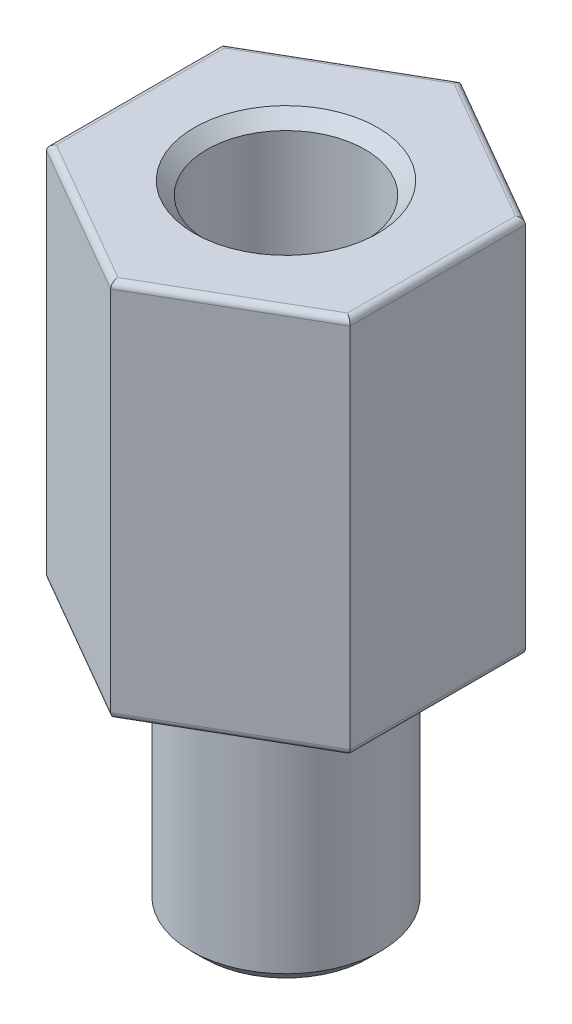
SolidWorks part; units mm, degrees
ref_plane "Спереди" through (0, 0, 0) normal (0, 0, 1) x (1, 0, 0)
ref_plane "Сверху" through (0, 0, 0) normal (0, 1, 0) x (1, 0, 0)
ref_plane "Справа" through (0, 0, 0) normal (1, 0, 0) x (0, 0, -1)
sketch "Эскиз2" plane through (0, 0, 0) normal (0, 1, 0) x (1, 0, 0)
  circle A0 centre (0, 0) radius 1.5
  dimension "D1" = 3
extrude "Бобышка-Вытянуть1" add sketch "Эскиз2" along normal blind 4
cosmetic thread "Условное изображение резьбы1" parameters "D1"=4, "D2"=2.621
sketch "Эскиз3" plane through (0, 4, 0) normal (0, 1, 0) x (1, 0, 0)
  line L1 (-2.4, 1.3856) -> (-2.4, -1.3856)
  line L2 (-2.4, -1.3856) -> (0, -2.7713)
  line L3 (0, -2.7713) -> (2.4, -1.3856)
  line L4 (2.4, -1.3856) -> (2.4, 1.3856)
  line L5 (2.4, 1.3856) -> (0, 2.7713)
  line L6 (0, 2.7713) -> (-2.4, 1.3856)
  circle A1 centre (0, 0) radius 2.4 construction
  dimension "D1" = 4.8
extrude "Бобышка-Вытянуть2" add sketch "Эскиз3" along normal blind 6
fillet "Скругление1" radius 0.1 12 edges at (2.4, 4, 0) (1.2, 4, 2.0785) (-1.2, 4, 2.0785) (-2.4, 4, 0) (-1.2, 4, -2.0785) (1.2, 4, -2.0785) (-1.2, 10, -2.0785) (-2.4, 10, 0) (-1.2, 10, 2.0785) (1.2, 10, 2.0785) (2.4, 10, 0) (1.2, 10, -2.0785)
sketch "Эскиз4" plane through (0, 10, 0) normal (0, 1, 0) x (1, 0, 0)
  circle A2 centre (0, 0) radius 1.5
  circle A3 centre (0, 0) radius 1.5
  dimension "D1" = 0
hole_wizard "Отверстие обработанное метчиком M31" positions "Трехмерный эскиз1" profile "Эскиз5" tap size "M3" standard "ГОСТ"
sketch3d "Трехмерный эскиз1"
  point P0 (0, 10, 0)
sketch "Эскиз5" plane through (0, 10, 0) normal (1, 0, 0) x (0, 0, 1)
  line L0 (0, 0) -> (0, 5.7511)
  line L1 (0, 5.7511) -> (1.25, 5)
  line L2 (1.25, 5) -> (1.25, 0)
  line L5 (1.25, 0) -> (0, 0)
  line L10 (0, 5.7511) -> (-1.25, 5) construction
  line L11 (0, -6.35) -> (0, 107.95) construction
  dimension "Диаметр сверла" = 2.5
  dimension "Глубина сверла" = 5
  dimension "Угол заточки сверла" = 118
cosmetic thread "Отверстие резьбы1" parameters "D1"=5, "D2"=3
chamfer "Фаска2" distance 0.2 angle 45 2 edges at (0, 0, 1.5) (0, 10, 1.25)
